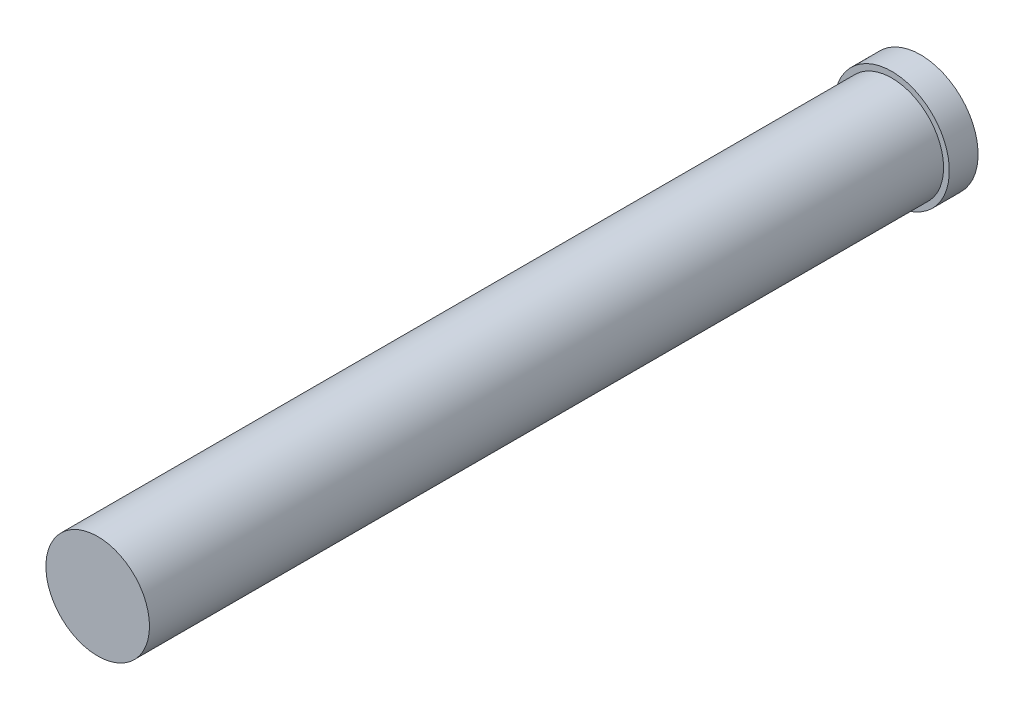
SolidWorks part; units mm, degrees
ref_plane "Front Plane" through (0, 0, 0) normal (0, 0, 1) x (1, 0, 0)
ref_plane "Top Plane" through (0, 0, 0) normal (0, 1, 0) x (1, 0, 0)
ref_plane "Right Plane" through (0, 0, 0) normal (1, 0, 0) x (0, 0, -1)
sketch "Sketch1" plane through (0, 0, 0) normal (0, 0, 1) x (1, 0, 0)
  circle A0 centre (0, 0) radius 2.286
  dimension "D1" = 4.572
extrude "Boss-Extrude1" add sketch "Sketch1" against normal mid plane 35.052
sketch "Sketch2" plane through (0, 0, -17.526) normal (0, 0, -1) x (-1, 0, 0)
  circle A0 centre (0, 0) radius 2.54
  dimension "D1" = 5.08
extrude "Boss-Extrude2" add sketch "Sketch2" along normal blind 1.27
